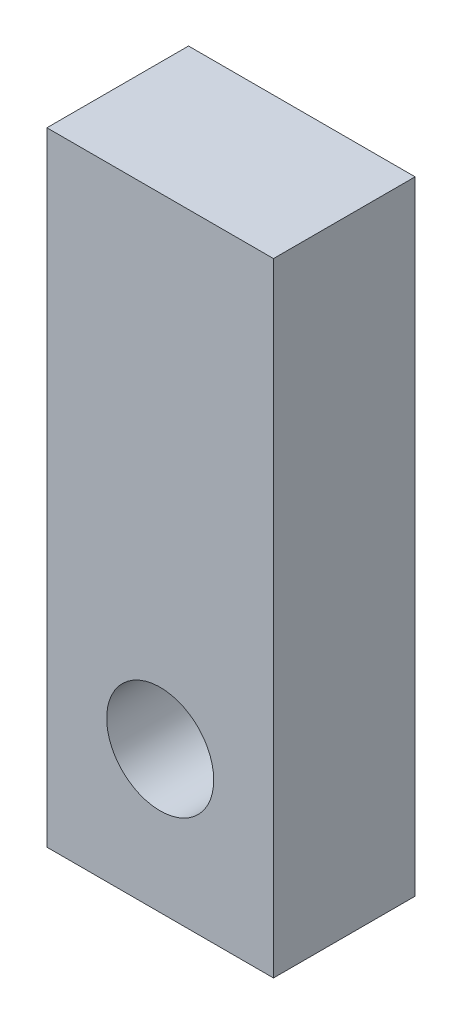
SolidWorks part; units mm, degrees
material "1.0037 (S235JR)"
ref_plane "Vorne" through (0, 0, 0) normal (0, 0, 1) x (1, 0, 0)
ref_plane "Oben" through (0, 0, 0) normal (0, 1, 0) x (1, 0, 0)
ref_plane "Rechts" through (0, 0, 0) normal (1, 0, 0) x (0, 0, -1)
sketch "Skizze1" plane through (0, 0, 0) normal (0, 0, 1) x (1, 0, 0)
  line L1 (-4, -5) -> (4, -5)
  line L2 (-4, -5) -> (-4, 17)
  line L3 (-4, 17) -> (4, 17)
  line L4 (4, -5) -> (4, 17)
  circle A0 centre (0, 0) radius 1.89 construction
  dimension "D4" = 3.78
  dimension "D1" = 4
  dimension "D2" = 8
  dimension "D3" = 5
  dimension "D5" = 17
extrude "Aufsatz-Linear austragen1" add sketch "Skizze1" along normal blind 5
hole_wizard "M4 Gewindebohrung1" positions "Skizze3" profile "Skizze2" tap size "M4" standard "Iso" end condition through all
sketch "Skizze3" plane through (0, 0, 5) normal (0, 0, 1) x (1, 0, 0)
  point P0 (0, 0)
sketch "Skizze2" plane through (0, 0, 5) normal (1, 0, 0) x (0, -1, 0)
  line L0 (0, 0) -> (0, 5)
  line L1 (0, 5) -> (1.89, 5)
  line L2 (1.89, 5) -> (1.89, 0)
  line L5 (1.89, 0) -> (0, 0)
  line L11 (0, -6.35) -> (0, 107.95) construction
  dimension "Bohrerdurchmesser" = 3.78
  dimension "Bohrungstiefe" = 5
cosmetic thread "Bohrungsgewinde1" parameters "D2"=4
move or copy body "Körper-Verschieben/Kopieren1" [suppressed] bodies to move or copy 104
